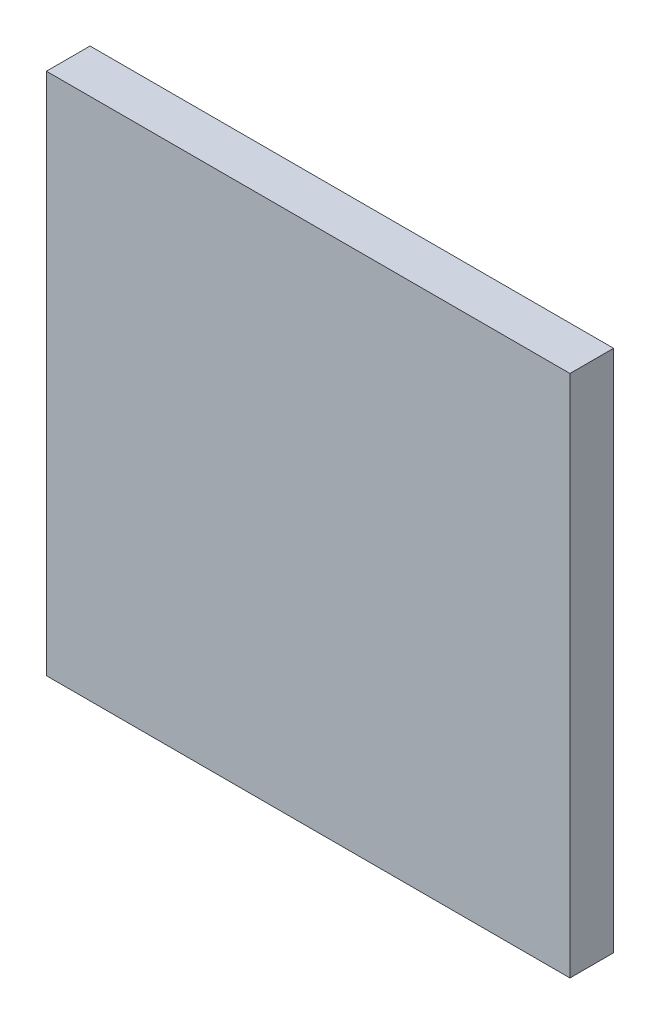
SolidWorks part; units mm, degrees
ref_plane "Front Plane" through (0, 0, 0) normal (0, 0, 1) x (1, 0, 0)
ref_plane "Top Plane" through (0, 0, 0) normal (0, 1, 0) x (1, 0, 0)
ref_plane "Right Plane" through (0, 0, 0) normal (1, 0, 0) x (0, 0, -1)
sketch "Sketch1" plane through (0, 0, 0) normal (0, 0, 1) x (1, 0, 0)
  line L1 (-152.4, -152.4) -> (152.4, -152.4)
  line L2 (-152.4, -152.4) -> (-152.4, 152.4)
  line L3 (-152.4, 152.4) -> (152.4, 152.4)
  line L4 (152.4, -152.4) -> (152.4, 152.4)
  line L5 (0, 152.4) -> (0, -152.4) construction
  line L6 (-152.4, 0) -> (152.4, 0) construction
  point P0 (0, 0)
  dimension "D1" = 304.8
  dimension "D2" = 304.8
extrude "Boss-Extrude1" add sketch "Sketch1" along normal blind 25.4
